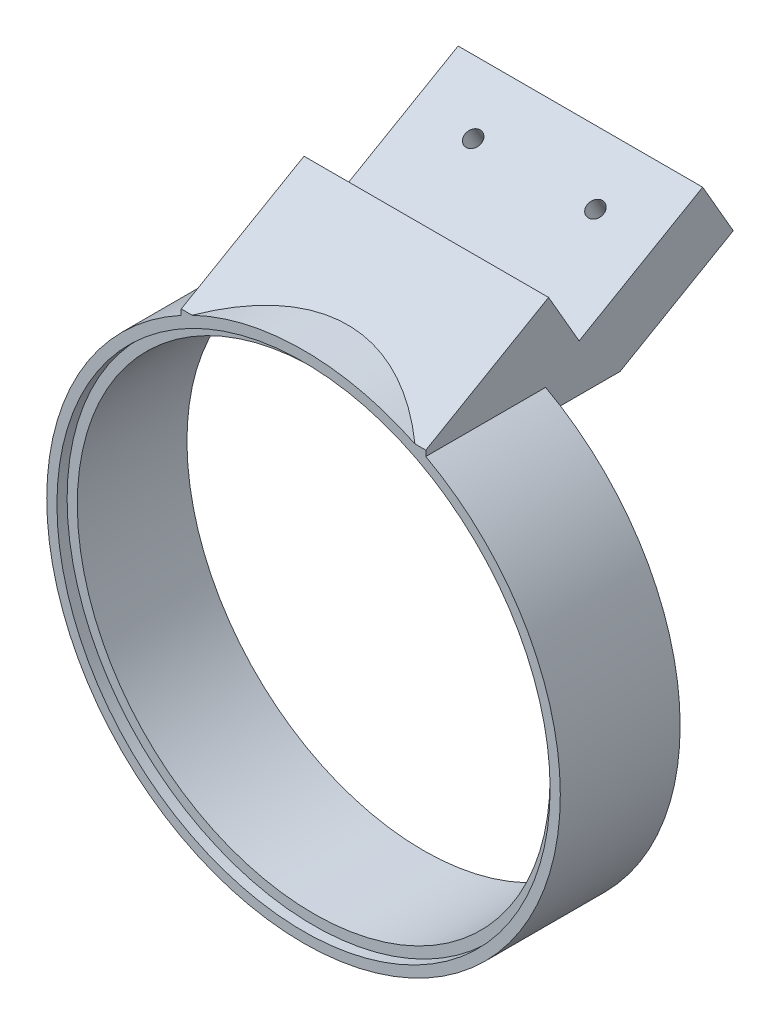
SolidWorks part; units mm, degrees
material "ABS"
ref_plane "Front Plane" through (0, 0, 0) normal (0, 0, 1) x (1, 0, 0)
ref_plane "Top Plane" through (0, 0, 0) normal (0, 1, 0) x (1, 0, 0)
ref_plane "Right Plane" through (0, 0, 0) normal (1, 0, 0) x (0, 0, -1)
sketch "Sketch1" plane through (0, 0, 0) normal (0, 0, 1) x (1, 0, 0)
  circle A0 centre (0, 0) radius 58
  circle A1 centre (0, 0) radius 63
  dimension "D1" = 116
  dimension "D2" = 5
extrude "Boss-Extrude1" add sketch "Sketch1" along normal blind 29.4
sketch "Sketch2" plane through (0, 0, 29.4) normal (0, 0, 1) x (1, 0, 0)
  circle A0 centre (0, 0) radius 58
  circle A1 centre (0, 0) radius 60.5
  circle A2 centre (0, 0) radius 58 construction
  dimension "D1" = 2.5
extrude "Cut-Extrude1" cut sketch "Sketch2" against normal blind 2
sketch "Sketch3" plane through (0, 0, 0) normal (0, 1, 0) x (1, 0, 0)
  line L0 (63, 0) -> (-63, 0) construction
  line L1 (-30, -29.4) -> (30, -29.4)
  line L2 (-30, -29.4) -> (-30, 0)
  line L3 (-30, 0) -> (30, 0)
  line L4 (30, -29.4) -> (30, 0)
  line L5 (-30, -29.4) -> (30, 0) construction
  line L6 (-30, 0) -> (30, -29.4) construction
  point P0 (0, -14.7)
  dimension "D1" = 29.4
  dimension "D2" = 60
extrude "Boss-Extrude2" add sketch "Sketch3" along normal blind 20 from surface starting at face at (63, 0, 29.4)
sketch "Sketch5" plane through (-30, 0, 0) normal (-1, 0, 0) x (0, 0, 1)
  line L0 (0, 75.3986) -> (0, 99.8623)
  line L1 (0, 99.8623) -> (29.4, 99.8623)
  line L2 (29.4, 99.8623) -> (29.4, 75.3986)
  line L3 (29.4, 75.3986) -> (0, 75.3986)
extrude "Cut-Extrude2" cut sketch "Sketch5" against normal up to surface (60 mm away) up to face at (30, 65.3986, 14.7)
sketch "Sketch6" plane through (-30, 0, 0) normal (-1, 0, 0) x (0, 0, 1)
  line L3 (0, 75.3986) -> (29.4, 126.3208)
  line L4 (29.4, 126.3208) -> (29.4, 75.3986)
  line L5 (29.4, 75.3986) -> (0, 75.3986)
  dimension "D1" = 60
extrude "Boss-Extrude3" add sketch "Sketch6" against normal up to surface (60 mm away) up to face at (30, 65.3986, 14.7)
sketch "Sketch7" plane through (0, 18.8496, -32.6485) normal (0, 0.5, -0.866) x (1, 0, 0)
  line L4 (-30, -124.0971) -> (30, -124.0971)
  line L5 (30, -124.0971) -> (30, -65.2971)
  line L6 (30, -65.2971) -> (-30, -65.2971)
  line L7 (-30, -65.2971) -> (-30, -124.0971)
  line L8 (-30, -124.0971) -> (30, -124.0971)
  line L9 (30, -124.0971) -> (30, -65.2971)
  line L10 (30, -65.2971) -> (-30, -65.2971)
  line L11 (-30, -65.2971) -> (-30, -124.0971)
  dimension "D1" = 0
extrude "Boss-Extrude4" add sketch "Sketch7" along normal blind 50
sketch "Sketch8" plane through (30, 0, 0) normal (1, 0, 0) x (0, 0, -1)
  line L0 (28.6013, 125.8597) -> (-29.4, 92.3727)
  line L1 (13.9013, 151.3208) -> (43.3013, 100.3986) construction
  line L2 (-29.4, 55.3986) -> (-29.4, 126.3208) construction
  line L3 (-29.4, 92.3727) -> (-29.4, 126.3208)
  line L4 (-29.4, 126.3208) -> (13.9013, 151.3208)
  line L5 (13.9013, 151.3208) -> (28.6013, 125.8597)
  line L6 (43.3013, 100.3986) -> (0, 75.3986) construction
  dimension "D1" = 29.4
extrude "Cut-Extrude3" cut sketch "Sketch8" against normal up to next
sketch "Sketch9" plane through (0, 56.5489, 32.6485) normal (0, -0.866, -0.5) x (1, 0, 0)
  line L4 (30, -37.6993) -> (-30, -37.6993)
  line L5 (-30, -37.6993) -> (-30, -87.6993)
  line L6 (-30, -87.6993) -> (30, -87.6993)
  line L7 (30, -87.6993) -> (30, -37.6993)
  line L8 (30, -37.6993) -> (-30, -37.6993)
  line L9 (-30, -37.6993) -> (-30, -87.6993)
  line L10 (-30, -87.6993) -> (30, -87.6993)
  line L11 (30, -87.6993) -> (30, -37.6993)
  dimension "D1" = 0
extrude "Boss-Extrude5" add sketch "Sketch9" along normal blind 31.44
sketch "Sketch10" plane through (0, 18.8496, -32.6485) normal (0, -0.5, 0.866) x (1, 0, 0)
  line L4 (30, 65.2971) -> (-30, 65.2971)
  line L5 (-30, 65.2971) -> (-30, 33.8571)
  line L6 (-30, 33.8571) -> (30, 33.8571)
  line L7 (30, 33.8571) -> (30, 65.2971)
  line L8 (30, 65.2971) -> (-30, 65.2971)
  line L9 (-30, 65.2971) -> (-30, 33.8571)
  line L10 (-30, 33.8571) -> (30, 33.8571)
  line L11 (30, 33.8571) -> (30, 65.2971)
  dimension "D1" = 0
extrude "Boss-Extrude6" add sketch "Sketch10" along normal blind 30
sketch "Sketch11" plane through (0, 0, 29.4) normal (0, 0, 1) x (1, 0, 0)
  circle A0 centre (0, 0) radius 58
  circle A1 centre (0, 0) radius 58 construction
extrude "Cut-Extrude4" cut sketch "Sketch11" against normal through all
sketch "Sketch14" plane through (0, 0, 29.4) normal (0, 0, 1) x (1, 0, 0)
  line L0 (-30, 55.3986) -> (-30, 142.9473)
  line L1 (-30, 142.9473) -> (30, 142.9473)
  line L2 (30, 142.9473) -> (30, 55.3986)
  line L3 (30, 55.3986) -> (30, 142.9473)
  arc A0 (30, 55.3986) -> (-30, 55.3986) centre (0, 0) ccw
  line M1 (30, 92.3727) -> (-30, 92.3727)
  line M2 (-30, 92.3727) -> (-30, 55.3986)
  line M4 (30, 55.3986) -> (30, 92.3727)
extrude "Cut-Extrude5" cut sketch "Sketch14" against normal blind 14.7 contours L2 L1 L0 M1 | A0 M4 M1 M2
sketch "Sketch15" plane through (30, 0, 0) normal (1, 0, 0) x (0, 0, -1)
  line L0 (44.0213, 99.1515) -> (-14.7, 65.2487)
  line L1 (28.6013, 125.8597) -> (59.0213, 73.1707) construction
  line L3 (-14.7, 65.2487) -> (-14.7, 100.8597)
  line L4 (-14.7, 100.8597) -> (28.6013, 125.8597)
  line L5 (28.6013, 125.8597) -> (44.0213, 99.1515)
  line L6 (59.0213, 73.1707) -> (18.2626, 49.6387) construction
  line L7 (-14.7, 100.8597) -> (-14.7, 55.3986) construction
  dimension "D1" = 30
extrude "Cut-Extrude6" cut sketch "Sketch15" against normal up to next
sketch "Sketch16" plane through (30, 0, 0) normal (1, 0, 0) x (0, 0, -1)
  line L1 (-17.9046, 55.3986) -> (-14.7, 55.3986)
  line L2 (-14.7, 55.3986) -> (-14.7, 65.2487)
  line L3 (-14.7, 65.2487) -> (-17.9046, 63.3986)
  line L5 (-14.7, 65.2487) -> (44.0213, 99.1515) construction
  line L7 (-17.9046, 63.3986) -> (-17.9046, 55.3986)
  dimension "D1" = 8
extrude "Boss-Extrude7" add sketch "Sketch16" against normal up to surface (60 mm away) up to face at (-30, 63.9493, -13.1293)
sketch "Sketch25" plane through (30, 0, 0) normal (1, 0, 0) x (0, 0, -1)
  line L0 (-17.9046, 55.3986) -> (-31.761, 55.3986)
  line L1 (-31.761, 55.3986) -> (-17.9046, 63.3986)
  line L2 (-17.9046, 63.3986) -> (-17.9046, 55.3986)
  line L3 (-17.9046, 63.3986) -> (44.0213, 99.1515) construction
extrude "Boss-Extrude10" add sketch "Sketch25" against normal up to surface (60 mm away) up to face at (-30, 63.685, -12.2137)
sketch "Sketch17" plane through (0, 0, 29.4) normal (0, 0, 1) x (1, 0, 0)
  circle A0 centre (0, 0) radius 58
  arc A1 (-17.1756, 55.3986) -> (17.1756, 55.3986) centre (0, 0) ccw construction
extrude "Cut-Extrude7" cut sketch "Sketch17" against normal through all and the other way through all
sketch "Sketch26" plane through (0, 0, 29.4) normal (0, 0, 1) x (1, 0, 0)
  circle A0 centre (0, 0) radius 60.5
  circle A1 centre (0, 0) radius 57.5
  arc A2 (-24.3156, 55.3986) -> (24.3156, 55.3986) centre (0, 0) ccw construction
extrude "Cut-Extrude13" cut sketch "Sketch26" along normal blind 10 from offset 2.5 contours A1 | A0 offset against normal yes
sketch "Sketch27" plane through (0, 0, 29.4) normal (0, 0, 1) x (1, 0, 0)
  circle A0 centre (0, 0) radius 60.5
  circle A1 centre (0, 0) radius 63
  arc A2 (-30, 55.3986) -> (30, 55.3986) centre (0, 0) ccw construction
  circle A3 centre (0, 0) radius 60.5 construction
extrude "Cut-Extrude14" cut sketch "Sketch27" along normal blind 10
sketch "Sketch28" plane through (0, 0, 29.4) normal (0, 0, 1) x (1, 0, 0)
  circle A0 centre (0, 0) radius 82.178
extrude "Cut-Extrude15" cut sketch "Sketch28" along normal blind 10
sketch "Sketch18" plane through (0, 43.8496, -75.9498) normal (0, 0.5, -0.866) x (1, 0, 0)
  line L0 (-30, -63.8571) -> (30, -63.8571) construction
  line L1 (-30, -63.8571) -> (30, -63.8571)
  line L2 (-30, -63.8571) -> (-30, -48.8571)
  line L3 (-30, -48.8571) -> (30, -48.8571)
  line L4 (30, -63.8571) -> (30, -48.8571)
  line L5 (-30, -33.8571) -> (30, -33.8571) construction
  dimension "D1" = 15
extrude "Cut-Extrude8" cut sketch "Sketch18" against normal blind 50
sketch "Sketch29" plane through (0, 29.3211, 16.9285) normal (0, -0.866, -0.5) x (1, 0, 0)
  circle A4 centre (-15, -59.6369) radius 2
  circle A5 centre (15, -59.6369) radius 2
  dimension "D1" = 4
  dimension "D2" = 4
extrude "Cut-Extrude16" cut sketch "Sketch29" against normal up to surface (15 mm away) up to face at (0, 73.6611, -29.8706)
sketch "Sketch30" plane through (0, 42.3115, 24.4285) normal (0, 0.866, 0.5) x (1, 0, 0)
  line L0 (30, 37.6993) -> (30, 87.6993) construction
  line L1 (-30, 87.6993) -> (30, 87.6993)
  line L2 (-30, 87.6993) -> (-30, 72.6993)
  line L3 (-30, 72.6993) -> (30, 72.6993)
  line L4 (30, 87.6993) -> (30, 72.6993)
  dimension "D1" = 15
extrude "Cut-Extrude17" cut sketch "Sketch30" against normal up to next
